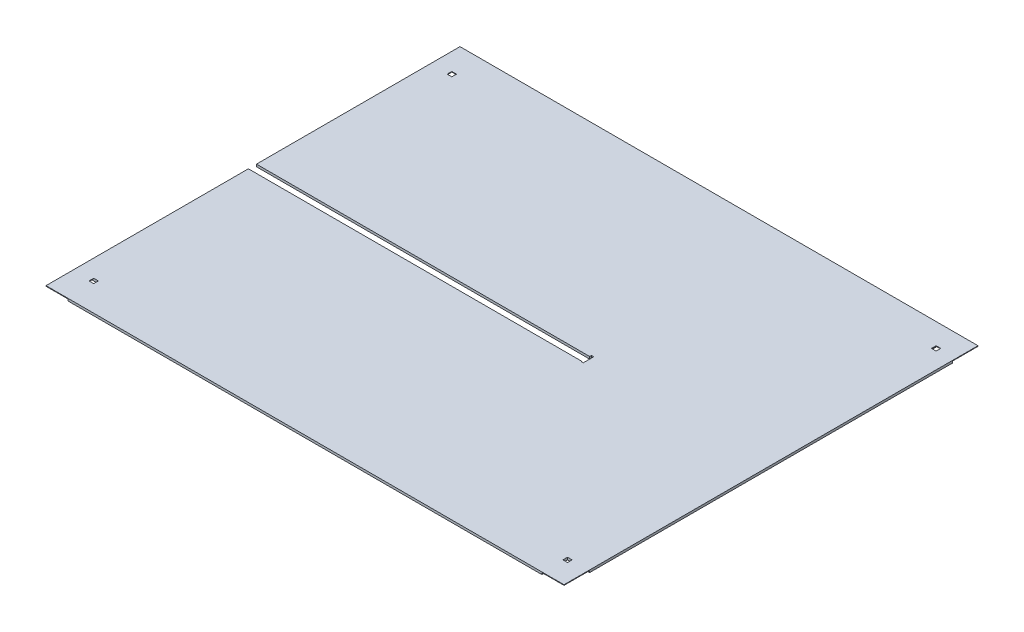
SolidWorks part; units mm, degrees
material "Pine"
ref_plane "Front Plane" through (0, 0, 0) normal (0, 0, 1) x (1, 0, 0)
ref_plane "Top Plane" through (0, 0, 0) normal (0, 1, 0) x (1, 0, 0)
ref_plane "Right Plane" through (0, 0, 0) normal (1, 0, 0) x (0, 0, -1)
sketch "Sketch1" plane through (0, 0, 0) normal (0, 1, 0) x (1, 0, 0)
  line L1 (1427.099, -1130.3) -> (-1427.099, -1130.3)
  line L2 (1427.099, -1130.3) -> (1427.099, 1130.3)
  line L3 (1427.099, 1130.3) -> (-1427.099, 1130.3)
  line L4 (-1427.099, -1130.3) -> (-1427.099, -25.146)
  line L5 (1427.099, -1130.3) -> (-1427.099, 1130.3) construction
  line L6 (1427.099, 1130.3) -> (-1427.099, -1130.3) construction
  line L7 (404.749, -28.448) -> (404.749, 28.702)
  line L8 (404.749, 28.702) -> (392.049, 28.702)
  line L9 (-1427.099, 19.05) -> (-1427.099, 1130.3)
  line L10 (392.049, 28.702) -> (392.049, 19.05)
  line L11 (392.049, 19.05) -> (-1427.099, 19.05)
  line L13 (392.049, -28.448) -> (392.049, -25.146)
  line L14 (392.049, -25.146) -> (-1427.099, -25.146)
  line L15 (392.049, -28.448) -> (404.749, -28.448)
  point P0 (0, 0)
  dimension "D1" = 2854.198
  dimension "D2" = 2260.6
  dimension "D3" = 3.302
  dimension "D4" = 57.15
  dimension "D5" = 1831.848
  dimension "D6" = 12.7
  dimension "D7" = 9.652
  dimension "D8" = 1101.852
extrude "Boss-Extrude1" add sketch "Sketch1" along normal blind 12.7
sketch "Sketch3" plane through (1427.099, 0, 0) normal (1, 0, 0) x (0, 0, -1)
  line L0 (-1130.3, 12.7) -> (1130.3, 12.7) construction
  line L1 (-1130.3, 9.525) -> (-990.6, 9.525)
  line L2 (-1130.3, 9.525) -> (-1130.3, 0)
  line L3 (-1130.3, 0) -> (-990.6, 0)
  line L4 (-990.6, 9.525) -> (-990.6, 0)
  line L5 (-1130.3, 9.525) -> (-990.6, 0) construction
  line L6 (-1130.3, 0) -> (-990.6, 9.525) construction
  line L7 (990.6, 9.525) -> (1130.3, 9.525)
  line L8 (990.6, 9.525) -> (990.6, 0)
  line L9 (990.6, 0) -> (1130.3, 0)
  line L10 (1130.3, 9.525) -> (1130.3, 0)
  line L11 (990.6, 9.525) -> (1130.3, 0) construction
  line L12 (990.6, 0) -> (1130.3, 9.525) construction
  point P0 (-1060.45, 4.7625)
  point P5 (1060.45, 4.7625)
  dimension "D1" = 3.175
  dimension "D2" = 139.7
  dimension "D3" = 3.175
  dimension "D4" = 139.7
extrude "Cut-Extrude2" cut sketch "Sketch3" against normal blind 146.05
sketch "Sketch4" plane through (-1427.099, 0, 0) normal (-1, 0, 0) x (0, 0, 1)
  line L0 (-1130.3, 12.7) -> (-19.05, 12.7) construction
  line L1 (1130.3, 0) -> (965.2, 0)
  line L2 (1130.3, 0) -> (1130.3, 9.525)
  line L3 (1130.3, 9.525) -> (965.2, 9.525)
  line L4 (965.2, 0) -> (965.2, 9.525)
  line L5 (1130.3, 0) -> (965.2, 9.525) construction
  line L6 (1130.3, 9.525) -> (965.2, 0) construction
  line L7 (-965.2, 0) -> (-1130.3, 0)
  line L8 (-965.2, 0) -> (-965.2, 9.525)
  line L9 (-965.2, 9.525) -> (-1130.3, 9.525)
  line L10 (-1130.3, 0) -> (-1130.3, 9.525)
  line L11 (-965.2, 0) -> (-1130.3, 9.525) construction
  line L12 (-965.2, 9.525) -> (-1130.3, 0) construction
  line L13 (25.146, 12.7) -> (1130.3, 12.7) construction
  point P0 (1047.75, 4.7625)
  point P5 (-1047.75, 4.7625)
  dimension "D1" = 3.175
  dimension "D2" = 165.1
  dimension "D3" = 165.1
  dimension "D4" = 3.175
extrude "Cut-Extrude3" cut sketch "Sketch4" against normal blind 120.65
sketch "Sketch5" plane through (0, 9.525, 0) normal (0, -1, 0) x (1, 0, 0)
  line L0 (1281.049, -1130.3) -> (1281.049, -990.6) construction
  line L1 (-1331.849, 990.6) -> (-1306.449, 990.6)
  line L2 (-1331.849, 990.6) -> (-1331.849, 965.2)
  line L3 (-1331.849, 965.2) -> (-1306.449, 965.2)
  line L4 (-1306.449, 990.6) -> (-1306.449, 965.2)
  line L5 (-1331.849, 990.6) -> (-1306.449, 965.2) construction
  line L6 (-1331.849, 965.2) -> (-1306.449, 990.6) construction
  line L7 (-1306.449, -965.2) -> (-1331.849, -965.2)
  line L8 (-1306.449, -965.2) -> (-1306.449, -990.6)
  line L9 (-1306.449, -990.6) -> (-1331.849, -990.6)
  line L10 (-1331.849, -965.2) -> (-1331.849, -990.6)
  line L11 (-1306.449, -965.2) -> (-1331.849, -990.6) construction
  line L12 (-1306.449, -990.6) -> (-1331.849, -965.2) construction
  line L13 (1312.799, -990.6) -> (1287.399, -990.6)
  line L14 (1312.799, -990.6) -> (1312.799, -1016)
  line L15 (1312.799, -1016) -> (1287.399, -1016)
  line L16 (1287.399, -990.6) -> (1287.399, -1016)
  line L17 (1312.799, -990.6) -> (1287.399, -1016) construction
  line L18 (1312.799, -1016) -> (1287.399, -990.6) construction
  line L19 (1306.449, 1016) -> (1281.049, 1016)
  line L20 (1306.449, 1016) -> (1306.449, 990.6)
  line L21 (1306.449, 990.6) -> (1281.049, 990.6)
  line L22 (1281.049, 1016) -> (1281.049, 990.6)
  line L23 (1306.449, 1016) -> (1281.049, 990.6) construction
  line L24 (1306.449, 990.6) -> (1281.049, 1016) construction
  line L25 (1281.049, -990.6) -> (1427.099, -990.6) construction
  point P0 (-1319.149, 977.9)
  point P7 (1300.099, -1003.3)
  point P8 (-1319.149, -977.9)
  point P19 (1293.749, 1003.3)
  dimension "D1" = 25.4
  dimension "D2" = 25.4
  dimension "D3" = 25.4
  dimension "D4" = 25.4
  dimension "D5" = 25.4
  dimension "D6" = 25.4
  dimension "D7" = 25.4
  dimension "D8" = 25.4
  dimension "D9" = 19.05
extrude "Cut-Extrude4" cut sketch "Sketch5" against normal up to surface (3.175 mm away) up to face at (-39.7087, 12.7, 0.9737)
sketch "Sketch6" plane through (0, 12.7, 0) normal (0, 1, 0) x (1, 0, 0)
  line L1 (1427.099, 1130.3) -> (1401.699, 1130.3)
  line L2 (1427.099, 1130.3) -> (1427.099, -1130.3)
  line L3 (1427.099, -1130.3) -> (1401.699, -1130.3)
  line L4 (1401.699, 1130.3) -> (1401.699, -1130.3)
  line L5 (1427.099, 1130.3) -> (1401.699, -1130.3) construction
  line L6 (1427.099, -1130.3) -> (1401.699, 1130.3) construction
  line L7 (1427.099, 1130.3) -> (-1427.099, 1130.3) construction
  line L8 (-1427.099, -1130.3) -> (1427.099, -1130.3) construction
  line L9 (1427.099, -1130.3) -> (1427.099, 1130.3) construction
  point P0 (1414.399, 0)
  dimension "D1" = 25.4
extrude "Cut-Extrude5" cut sketch "Sketch6" against normal up to surface (12.7 mm away) up to face at (-28.9052, 0, 0.5842)
